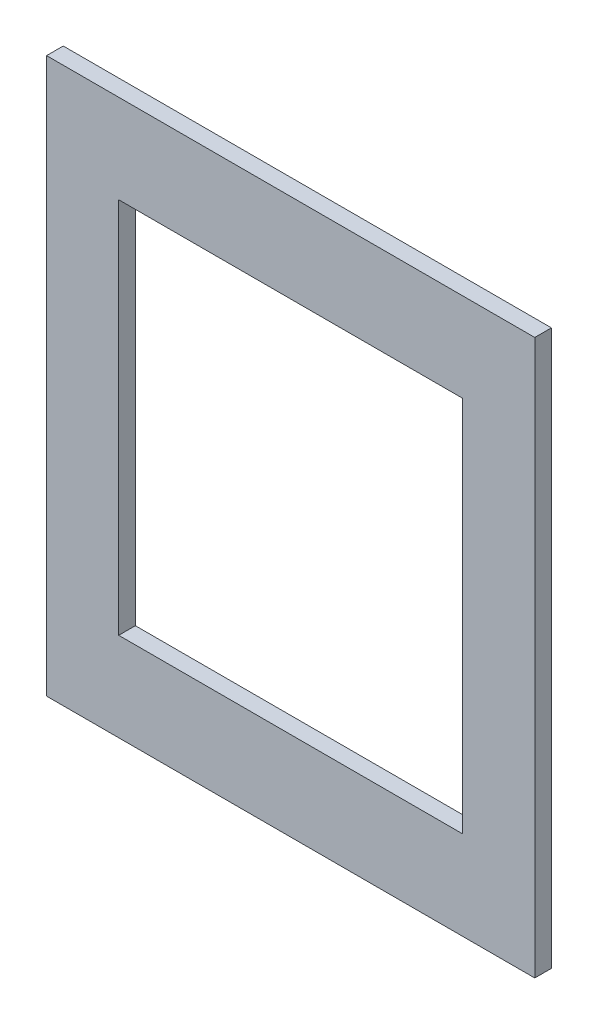
SolidWorks part; units mm, degrees
material "Plain Carbon Steel"
ref_plane "Wasteboard" through (0, 0, 0) normal (0, 0, 1) x (1, 0, 0)
ref_plane "Left-Right" through (0, 0, 0) normal (0, 1, 0) x (1, 0, 0)
ref_plane "Front-Back" through (0, 0, 0) normal (1, 0, 0) x (0, 0, -1)
sketch "Sketch1" plane through (0, 0, 0) normal (0, 0, 1) x (1, 0, 0)
  line L1 (-22, 25) -> (22, 25)
  line L2 (-22, 25) -> (-22, -25)
  line L3 (-22, -25) -> (22, -25)
  line L4 (22, 25) -> (22, -25)
  line L5 (-22, 25) -> (22, -25) construction
  line L6 (-22, -25) -> (22, 25) construction
  line L7 (-15.5, 17) -> (15.5, 17)
  line L8 (-15.5, 17) -> (-15.5, -17)
  line L9 (-15.5, -17) -> (15.5, -17)
  line L10 (15.5, 17) -> (15.5, -17)
  line L11 (-15.5, 17) -> (15.5, -17) construction
  line L12 (-15.5, -17) -> (15.5, 17) construction
  point P0 (0, 0)
  point P6 (0, 0)
  dimension "D1" = 44
  dimension "D2" = 50
  dimension "D3" = 8
  dimension "D4" = 8
  dimension "D5" = 6.5
extrude "Boss-Extrude1" add sketch "Sketch1" along normal blind 1.5
